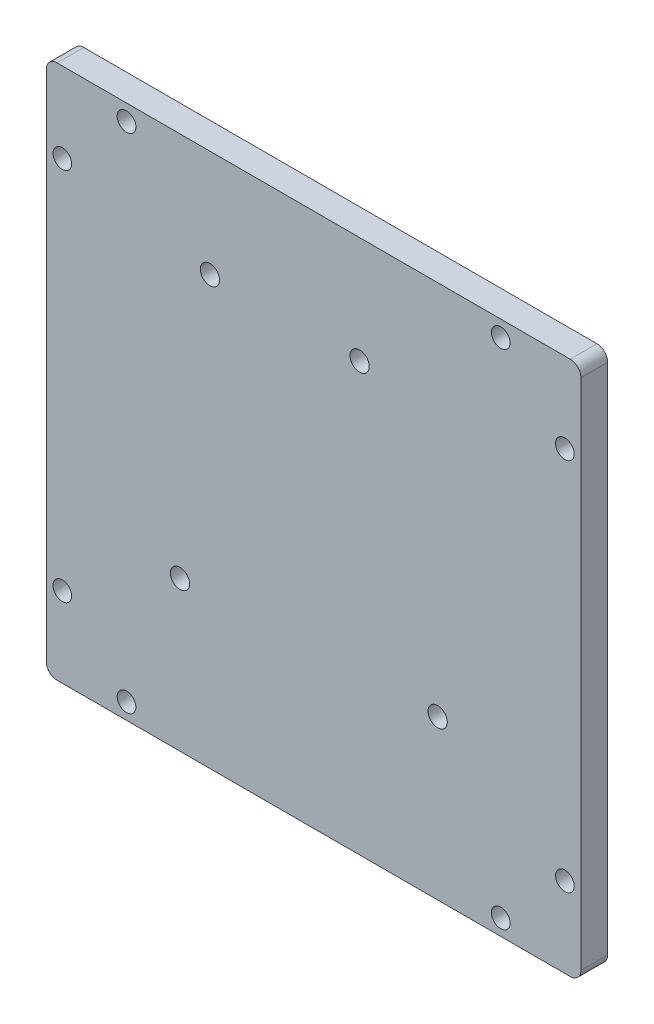
SolidWorks part; units mm, degrees
ref_plane "Спереди" through (0, 0, 0) normal (0, 0, 1) x (1, 0, 0)
ref_plane "Сверху" through (0, 0, 0) normal (0, 1, 0) x (1, 0, 0)
ref_plane "Справа" through (0, 0, 0) normal (1, 0, 0) x (0, 0, -1)
sketch "Эскиз1" plane through (0, 0, 0) normal (0, 0, 1) x (1, 0, 0)
  line L0 (0, 0) -> (27.9829, 0) construction
  line L1 (-48, -50) -> (48, -50)
  line L2 (-50, -48) -> (-50, 48)
  line L3 (-48, 50) -> (48, 50)
  line L4 (50, -48) -> (50, 48)
  line L5 (-50, -50) -> (50, 50) construction
  line L6 (-50, 50) -> (50, -50) construction
  line L7 (0, 0) -> (0, -40.6) construction
  line L8 (0, 50) -> (0, 30) construction
  line L9 (0, 30) -> (-27, 30) construction
  line L10 (0, 30) -> (27, 30) construction
  line L11 (-27, 30) -> (-19.4, 30) construction
  line L12 (-17.6, 30) -> (8.6, 30) construction
  line L13 (0, 30) -> (0, -20.3) construction
  circle A0 centre (-47, 35) radius 1.75
  circle A1 centre (47, 35) radius 1.75
  circle A2 centre (47, -35) radius 1.75
  circle A3 centre (-47, -35) radius 1.75
  circle A4 centre (-35, 47) radius 1.75
  circle A5 centre (35, 47) radius 1.75
  circle A6 centre (-35, -47) radius 1.75
  circle A7 centre (35, -47) radius 1.75
  arc A8 (-50, -48) -> (-48, -50) centre (-48, -48) ccw
  arc A9 (48, -50) -> (50, -48) centre (48, -48) ccw
  arc A10 (50, 48) -> (48, 50) centre (48, 48) ccw
  arc A11 (-48, 50) -> (-50, 48) centre (-48, 48) ccw
  circle A12 centre (-19.4, 30) radius 1.8
  circle A13 centre (8.6, 30) radius 1.8
  circle A14 centre (-25, -22) radius 1.8
  circle A15 centre (23.2, -20.3) radius 1.8
  point P0 (0, 0)
  dimension "D3" = 3.5
  dimension "D6" = 3.5
  dimension "D9" = 2
  dimension "D13" = 14.6
  dimension "D14" = 3.6
  dimension "D15" = 50.3
  dimension "D17" = 3.6
  dimension "D18" = 52
  dimension "D19" = 48.2
  dimension "D12" = 3.6
  dimension "D16" = 3.6
  dimension "D1" = 100
  dimension "D2" = 100
  dimension "D4" = 3
  dimension "D5" = 15
  dimension "D7" = 15
  dimension "D8" = 3
  dimension "D10" = 20
  dimension "D11" = 28
  dimension "D20" = 25
extrude "Бобышка-Вытянуть1" add sketch "Эскиз1" along normal blind 5
